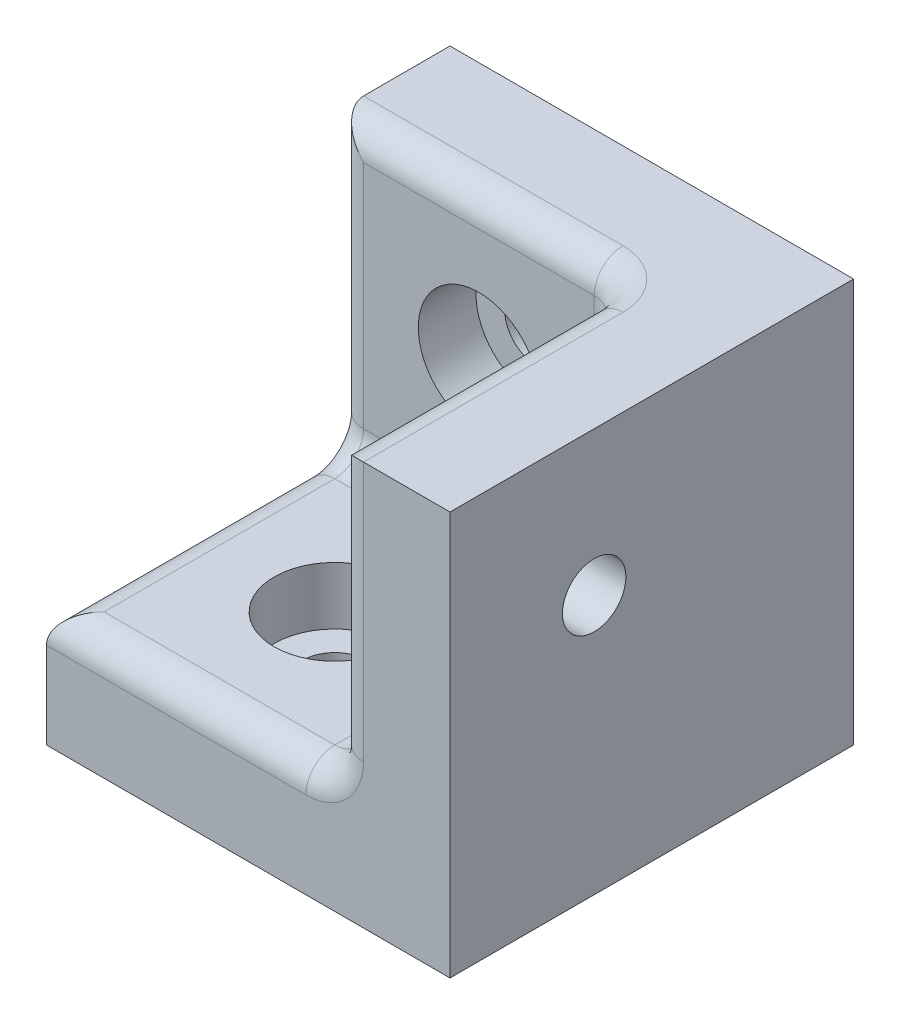
SolidWorks part; units mm, degrees
ref_plane "Plan de face" through (0, 0, 0) normal (0, 0, 1) x (1, 0, 0)
ref_plane "Plan de dessus" through (0, 0, 0) normal (0, 1, 0) x (1, 0, 0)
ref_plane "Plan de droite" through (0, 0, 0) normal (1, 0, 0) x (0, 0, -1)
sketch "Esquisse1" plane through (0, 0, 0) normal (0, 0, 1) x (1, 0, 0)
  line L1 (-5, 14) -> (5, 14)
  line L2 (-5, 14) -> (-5, 0)
  line L3 (-5, 0) -> (5, 0)
  line L4 (5, 14) -> (5, 0)
  dimension "D1" = 10
  dimension "D2" = 14
  dimension "D3" = 5
extrude "Boss.-Extru.1" add sketch "Esquisse1" along normal blind 4
sketch "Esquisse2" plane through (0, 0, 4) normal (0, 0, 1) x (1, 0, 0)
  line L0 (5, 0) -> (5, 14) construction
  line L1 (-5, 0) -> (5, 0)
  line L2 (-5, 0) -> (-5, 4)
  line L3 (-5, 4) -> (5, 4)
  line L4 (5, 0) -> (5, 4)
  dimension "D1" = 4
extrude "Boss.-Extru.2" add sketch "Esquisse2" along normal blind 10
sketch "Esquisse3" plane through (0, 0, 4) normal (0, 0, 1) x (1, 0, 0)
  line L0 (5, 14) -> (-5, 14) construction
  line L1 (-5, 14) -> (-5, 4) construction
  circle A0 centre (0, 9) radius 1.1
  point P2 (0, 14)
  point P3 (-5, 9)
  dimension "D1" = 2.2
extrude "Enlèv. mat.-Extru.1" cut sketch "Esquisse3" against normal through all
sketch "Esquisse4" plane through (0, 4, 0) normal (0, 1, 0) x (1, 0, 0)
  line L0 (5, -14) -> (-5, -14) construction
  line L1 (-5, -14) -> (-5, -4) construction
  circle A0 centre (0, -9) radius 1.1
  point P0 (0, -14)
  point P1 (-5, -9)
  dimension "D1" = 2.2
extrude "Enlèv. mat.-Extru.2" cut sketch "Esquisse4" against normal through all
sketch "Esquisse5" plane through (0, 0, 4) normal (0, 0, 1) x (1, 0, 0)
  circle A0 centre (0, 9) radius 2.1
  dimension "D1" = 4.2
extrude "Enlèv. mat.-Extru.3" cut sketch "Esquisse5" against normal blind 2
sketch "Esquisse6" plane through (0, 4, 0) normal (0, 1, 0) x (1, 0, 0)
  circle A0 centre (0, -9) radius 2.1
  dimension "D1" = 4.2
extrude "Enlèv. mat.-Extru.4" cut sketch "Esquisse6" against normal blind 2
sketch "Esquisse7" plane through (5, 0, 0) normal (1, 0, 0) x (0, 0, -1)
  line L0 (-14, 0) -> (-14, 14)
  line L1 (0, 14) -> (-14, 14)
  line L6 (0, 0) -> (0, 14)
  line L7 (0, 14) -> (-4, 14)
  line L8 (-4, 14) -> (-4, 4)
  line L9 (-4, 4) -> (-14, 4)
  line L10 (-14, 4) -> (-14, 0)
  line L11 (-14, 0) -> (0, 0)
  line L12 (0, 0) -> (0, 14)
  line L17 (-14, 0) -> (0, 0)
  dimension "D1" = 0
extrude "Boss.-Extru.3" add sketch "Esquisse7" along normal blind 4
sketch "Esquisse8" plane through (5, 0, 0) normal (-1, 0, 0) x (0, 0, 1)
  line L0 (4, 4) -> (4, 14) construction
  line L1 (14, 4) -> (4, 4) construction
  circle A0 centre (9, 9) radius 1.1
  point P2 (4, 9)
  point P3 (9, 4)
  dimension "D1" = 2.2
extrude "Enlèv. mat.-Extru.5" cut sketch "Esquisse8" against normal through all
sketch "Esquisse9" plane through (5, 0, 0) normal (-1, 0, 0) x (0, 0, 1)
  circle A0 centre (9, 9) radius 2.1
  dimension "D1" = 4.2
extrude "Enlèv. mat.-Extru.6" cut sketch "Esquisse9" against normal blind 2
fillet "Congé1" radius 1 9 edges at (0, 4, 4) (-5, 9, 4) (0, 4, 14) (-5, 4, 9) (0, 14, 4) (5, 14, 9) (5, 9, 14) (5, 9, 4) (5, 4, 9)
